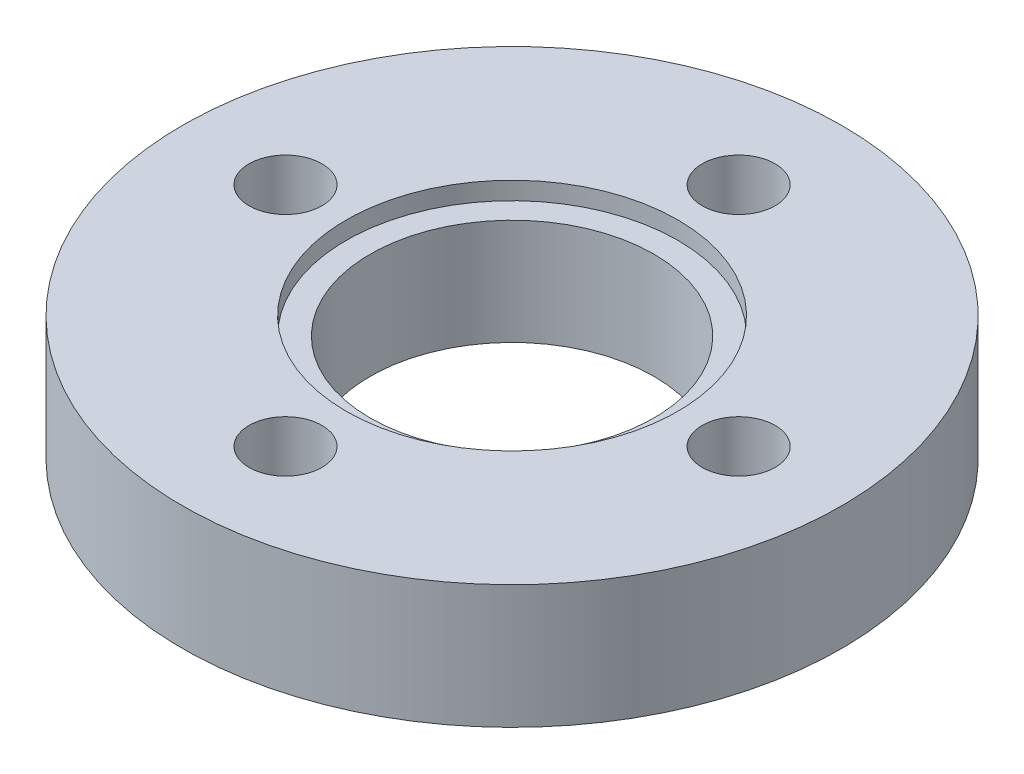
SolidWorks part; units mm, degrees
ref_plane "Front Plane" through (0, 0, 0) normal (0, 0, 1) x (1, 0, 0)
ref_plane "Top Plane" through (0, 0, 0) normal (0, 1, 0) x (1, 0, 0)
ref_plane "Right Plane" through (0, 0, 0) normal (1, 0, 0) x (0, 0, -1)
sketch "Sketch1" plane through (0, 0, 0) normal (0, 0, 1) x (1, 0, 0)
  line L0 (0, 0) -> (0, 25.4) construction
  line L1 (-20.32, 7.62) -> (-20.32, 0)
  line L2 (-8.7503, 0) -> (-20.32, 0)
  line L3 (-8.7503, 0) -> (-8.7503, 6.5278)
  line L4 (-8.7503, 6.5278) -> (-10.2235, 6.5278)
  line L8 (-20.32, 7.62) -> (-10.2235, 7.62)
  line L9 (-10.2235, 6.5278) -> (-10.2235, 7.62)
  dimension "D1" = 25.4
  dimension "D2" = 17.5006
  dimension "D3" = 7.62
  dimension "D4" = 20.447
  dimension "D5" = 1.0922
  dimension "D6" = 20.32
revolve "Revolve1" add sketch "Sketch1" angle 360 about L0
hole_wizard "#8 Clearance Hole1" positions "Sketch2" profile "Sketch3" hole size "#8" standard "ANSI Inch" end condition through all
sketch "Sketch2" plane through (0, 7.62, 0) normal (0, 1, 0) x (1, 0, 0)
  circle A0 centre (0, 0) radius 13.97
  point P6 (0, 13.97)
  point P8 (-13.97, 0)
  point P10 (0, -13.97)
  point P12 (13.97, 0)
  dimension "D1" = 27.94
sketch "Sketch3" plane through (13.97, 7.62, 0) normal (1, 0, 0) x (0, 0, 1)
  line L0 (0, 0) -> (0, 7.62)
  line L1 (0, 7.62) -> (2.2479, 7.62)
  line L2 (2.2479, 7.62) -> (2.2479, 0)
  line L5 (2.2479, 0) -> (0, 0)
  line L11 (0, -6.35) -> (0, 107.95) construction
  dimension "Thru Hole Dia." = 4.4958
  dimension "Thru Hole Depth" = 7.62
equation "\"outer diameter\"= 0.8"
equation "\"D6@Sketch1\"=\"outer diameter\""
